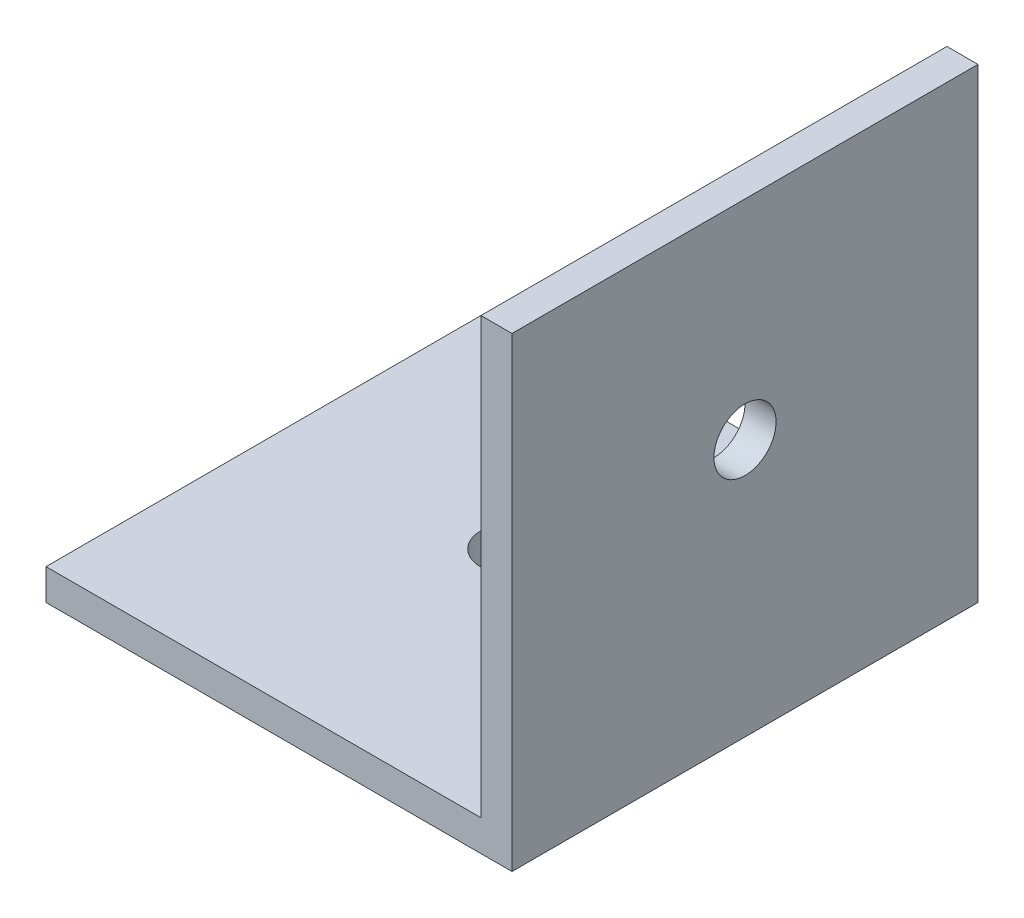
SolidWorks part; units mm, degrees
ref_plane "前视基准面" through (0, 0, 0) normal (0, 0, 1) x (1, 0, 0)
ref_plane "上视基准面" through (0, 0, 0) normal (0, 1, 0) x (1, 0, 0)
ref_plane "右视基准面" through (0, 0, 0) normal (1, 0, 0) x (0, 0, -1)
other "Configuration Table"
sketch "草图1" plane through (0, 0, 0) normal (0, 0, 1) x (1, 0, 0)
  line L0 (0, 0) -> (-15, 0)
  line L1 (-15, 0) -> (-15, 1)
  line L2 (-15, 1) -> (-1, 1)
  line L3 (-1, 1) -> (-1, 15)
  line L4 (-1, 15) -> (0, 15)
  line L5 (0, 15) -> (0, 0)
  dimension "D1" = 1
  dimension "D2" = 15
  dimension "D3" = 15
  dimension "D4" = 1
extrude "凸台-拉伸1" add sketch "草图1" along normal blind 15
sketch "草图2" plane through (-1, 0, 0) normal (-1, 0, 0) x (0, 0, 1)
  line L0 (0, 8.2883) -> (14.8765, 8.2883) construction
  line L2 (7.5, 15) -> (7.5, 8.1569) construction
  circle A0 centre (7.5, 8.2883) radius 1
extrude "切除-拉伸1" cut sketch "草图2" against normal through all
sketch "草图3" plane through (0, 1, 0) normal (0, 1, 0) x (1, 0, 0)
  line L0 (-15, -7.012) -> (0, -7.012) construction
  line L3 (-8, 0) -> (-8, -15) construction
  circle A0 centre (-8, -7.012) radius 1
extrude "切除-拉伸2" cut sketch "草图3" against normal through all
